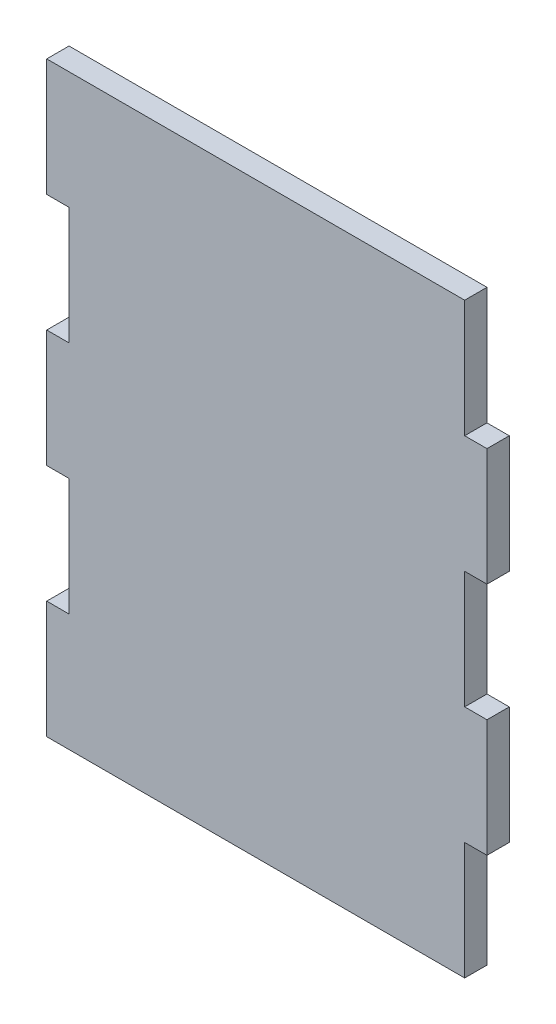
SolidWorks part; units mm, degrees
material "1060 Alloy"
ref_plane "Front Plane" through (0, 0, 0) normal (0, 0, 1) x (1, 0, 0)
ref_plane "Top Plane" through (0, 0, 0) normal (0, 1, 0) x (1, 0, 0)
ref_plane "Right Plane" through (0, 0, 0) normal (1, 0, 0) x (0, 0, -1)
sketch "Sketch1" plane through (0, 0, 0) normal (0, 0, 1) x (1, 0, 0)
  line L1 (-47.625, -63.5) -> (47.625, -63.5)
  line L2 (-47.625, -63.5) -> (-47.625, 63.5)
  line L3 (-47.625, 63.5) -> (47.625, 63.5)
  line L4 (47.625, -63.5) -> (47.625, 63.5)
  line L5 (-47.625, -63.5) -> (47.625, 63.5) construction
  line L6 (-47.625, 63.5) -> (47.625, -63.5) construction
  line L7 (-47.625, 38.1) -> (-42.799, 38.1)
  line L8 (-47.625, 38.1) -> (-47.625, 12.7)
  line L9 (-47.625, 12.7) -> (-42.799, 12.7)
  line L10 (-42.799, 38.1) -> (-42.799, 12.7)
  line L11 (-47.625, -12.7) -> (-42.799, -12.7)
  line L12 (-47.625, -12.7) -> (-47.625, -38.1)
  line L13 (-47.625, -38.1) -> (-42.799, -38.1)
  line L14 (-42.799, -12.7) -> (-42.799, -38.1)
  line L15 (47.625, 63.5) -> (42.799, 63.5)
  line L16 (47.625, 63.5) -> (47.625, 38.1)
  line L17 (47.625, 38.1) -> (42.799, 38.1)
  line L18 (42.799, 63.5) -> (42.799, 38.1)
  line L19 (47.625, 12.7) -> (42.799, 12.7)
  line L20 (47.625, 12.7) -> (47.625, -12.7)
  line L21 (47.625, -12.7) -> (42.799, -12.7)
  line L22 (42.799, 12.7) -> (42.799, -12.7)
  line L23 (47.625, -38.1) -> (42.799, -38.1)
  line L24 (47.625, -38.1) -> (47.625, -63.5)
  line L25 (47.625, -63.5) -> (42.799, -63.5)
  line L26 (42.799, -38.1) -> (42.799, -63.5)
  point P0 (0, 0)
  dimension "D1" = 95.25
  dimension "D2" = 127
  dimension "D3" = 4.826
extrude "Boss-Extrude1" add sketch "Sketch1" along normal blind 4.826 contours L26 L23 L4 L21 L22 L19 L17 L18 L3 L2 L7 L10 L9 L11 L14 L13 L1
equation "\"w\"= .19"
equation "\"D3@Sketch1\"=\"w\""
equation "\"D1@Boss-Extrude1\"=\"w\""
